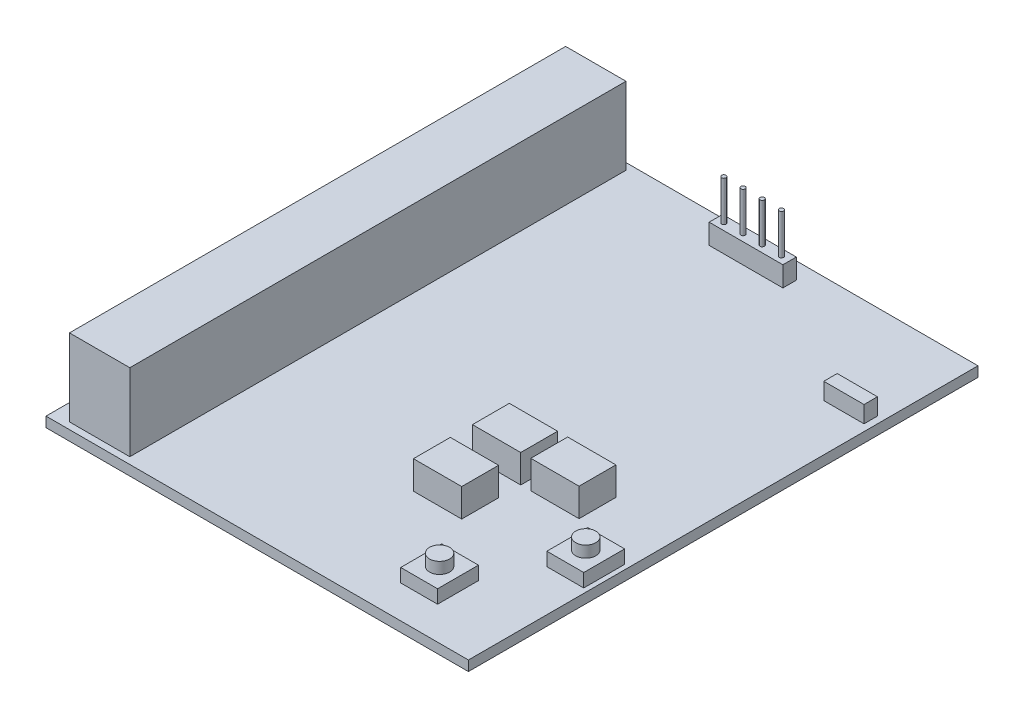
SolidWorks part; units mm, degrees
ref_plane "Front Plane" through (0, 0, 0) normal (0, 0, 1) x (1, 0, 0)
ref_plane "Top Plane" through (0, 0, 0) normal (0, 1, 0) x (1, 0, 0)
ref_plane "Right Plane" through (0, 0, 0) normal (1, 0, 0) x (0, 0, -1)
sketch "Sketch1" plane through (0, 0, 0) normal (0, 1, 0) x (1, 0, 0)
  line L1 (0, 0) -> (63, 0)
  line L2 (0, 0) -> (0, 76)
  line L3 (0, 76) -> (63, 76)
  line L4 (63, 0) -> (63, 76)
  dimension "D1" = 63
  dimension "D2" = 76
extrude "Boss-Extrude1" add sketch "Sketch1" along normal blind 1.5
sketch "Sketch2" plane through (0, 1.5, 0) normal (0, 1, 0) x (1, 0, 0)
  line L0 (63, 76) -> (0, 76) construction
  line L1 (2.5, 75) -> (11.5, 75)
  line L2 (2.5, 75) -> (2.5, 1)
  line L3 (2.5, 1) -> (11.5, 1)
  line L4 (11.5, 75) -> (11.5, 1)
  line L5 (0, 76) -> (0, 0) construction
  dimension "D1" = 74
  dimension "D2" = 1
  dimension "D3" = 2.5
  dimension "D4" = 9
extrude "Boss-Extrude2" add sketch "Sketch2" along normal blind 11.5
sketch "Sketch3" plane through (0, 0, 0) normal (0, -1, 0) x (1, 0, 0)
  line L0 (0, -76) -> (0, 0) construction
  line L1 (9, -15) -> (16, -15)
  line L2 (9, -15) -> (9, -23)
  line L3 (9, -23) -> (16, -23)
  line L4 (16, -15) -> (16, -23)
  line L5 (9, -34) -> (16, -34)
  line L6 (9, -34) -> (9, -42)
  line L7 (9, -42) -> (16, -42)
  line L8 (16, -34) -> (16, -42)
  line L9 (9, -56) -> (16, -56)
  line L10 (9, -56) -> (9, -64)
  line L11 (9, -64) -> (16, -64)
  line L12 (16, -56) -> (16, -64)
  line L13 (63, -76) -> (0, -76) construction
  dimension "D1" = 8
  dimension "D2" = 8
  dimension "D3" = 8
  dimension "D4" = 7
  dimension "D5" = 7
  dimension "D6" = 7
  dimension "D7" = 9
  dimension "D8" = 9
  dimension "D9" = 9
  dimension "D10" = 12
  dimension "D11" = 34
  dimension "D12" = 53
extrude "Boss-Extrude3" add sketch "Sketch3" along normal blind 3.5
sketch "Sketch4" plane through (0, 1.5, 0) normal (0, 1, 0) x (1, 0, 0)
  line L0 (63, 0) -> (63, 76) construction
  line L1 (27.4, 73.5) -> (38.4, 73.5)
  line L2 (27.4, 73.5) -> (27.4, 71.5)
  line L3 (27.4, 71.5) -> (38.4, 71.5)
  line L4 (38.4, 73.5) -> (38.4, 71.5)
  line L5 (63, 76) -> (0, 76) construction
  dimension "D1" = 11
  dimension "D2" = 2
  dimension "D3" = 24.6
  dimension "D4" = 2.5
extrude "Boss-Extrude4" add sketch "Sketch4" along normal blind 3
sketch "Sketch5" plane through (0, 4.5, 0) normal (0, 1, 0) x (1, 0, 0)
  line L0 (27.4, 73.5) -> (27.4, 71.5) construction
  line L1 (38.4, 73.5) -> (27.4, 73.5) construction
  circle A0 centre (28.6, 72.5) radius 0.325
  circle A1 centre (31.46, 72.5) radius 0.325
  circle A2 centre (34.32, 72.5) radius 0.325
  circle A3 centre (37.18, 72.5) radius 0.325
  dimension "D1" = 0.65
  dimension "D2" = 1.2
  dimension "D4" = 1
  dimension "D3" = 4
extrude "Boss-Extrude5" add sketch "Sketch5" along normal blind 6
sketch "Sketch6" plane through (0, 1.5, 0) normal (0, 1, 0) x (1, 0, 0)
  line L0 (63, 0) -> (63, 76) construction
  line L1 (56, 62) -> (62, 62)
  line L2 (56, 62) -> (56, 60)
  line L3 (56, 60) -> (62, 60)
  line L4 (62, 62) -> (62, 60)
  line L5 (63, 76) -> (0, 76) construction
  dimension "D1" = 6
  dimension "D2" = 2
  dimension "D3" = 1
  dimension "D4" = 14
extrude "Boss-Extrude6" add sketch "Sketch6" along normal blind 2.5
sketch "Sketch7" plane through (0, 4, 0) normal (0, 1, 0) x (1, 0, 0)
  line L0 (56, 62) -> (56, 60) construction
  circle A0 centre (57.5, 60.989) radius 0.4731
  circle A1 centre (60.4, 60.989) radius 0.4731
  dimension "D1" = 1.5
  dimension "D2" = 2
extrude "Boss-Extrude7" [suppressed] add sketch "Sketch7" along normal blind 6
sketch "Sketch8" plane through (0, 1.5, 0) normal (0, 1, 0) x (1, 0, 0)
  line L0 (63, 0) -> (63, 76) construction
  line L1 (37.1, 32) -> (44.3, 32)
  line L2 (37.1, 32) -> (37.1, 26.5)
  line L3 (37.1, 26.5) -> (44.3, 26.5)
  line L4 (44.3, 32) -> (44.3, 26.5)
  line L5 (45.8, 32) -> (53, 32)
  line L6 (45.8, 32) -> (45.8, 26.5)
  line L7 (45.8, 26.5) -> (53, 26.5)
  line L8 (53, 32) -> (53, 26.5)
  line L9 (37.1, 23.2) -> (44.3, 23.2)
  line L10 (37.1, 23.2) -> (37.1, 17.7)
  line L11 (37.1, 17.7) -> (44.3, 17.7)
  line L12 (44.3, 23.2) -> (44.3, 17.7)
  line L13 (0, 0) -> (63, 0) construction
  dimension "D1" = 7.2
  dimension "D2" = 7.2
  dimension "D3" = 7.2
  dimension "D4" = 5.5
  dimension "D5" = 5.5
  dimension "D6" = 5.5
  dimension "D7" = 10
  dimension "D8" = 18.7
  dimension "D9" = 18.7
  dimension "D10" = 17.7
  dimension "D11" = 26.5
  dimension "D12" = 26.5
extrude "Boss-Extrude8" add sketch "Sketch8" along normal blind 4.2
sketch "Sketch9" plane through (0, 1.5, 0) normal (0, 1, 0) x (1, 0, 0)
  line L0 (63, 0) -> (63, 76) construction
  line L1 (56.8, 24) -> (62.3, 24)
  line L2 (56.8, 24) -> (56.8, 17.9)
  line L3 (56.8, 17.9) -> (62.3, 17.9)
  line L4 (62.3, 24) -> (62.3, 17.9)
  line L5 (0, 0) -> (63, 0) construction
  dimension "D1" = 0.7
  dimension "D2" = 6.1
  dimension "D3" = 17.9
  dimension "D4" = 5.5
extrude "Boss-Extrude9" add sketch "Sketch9" along normal blind 2
sketch "Sketch10" plane through (0, 3.5, 0) normal (0, 1, 0) x (1, 0, 0)
  line L0 (62.3, 17.9) -> (62.3, 24) construction
  line L1 (62.3, 24) -> (56.8, 24) construction
  circle A0 centre (59.55, 20.95) radius 1.5
  dimension "D1" = 3
  dimension "D2" = 2.75
  dimension "D3" = 3.05
extrude "Boss-Extrude10" add sketch "Sketch10" along normal blind 1.7
sketch "Sketch11" plane through (0, 1.5, 0) normal (0, 1, 0) x (1, 0, 0)
  line L0 (63, 0) -> (63, 76) construction
  line L1 (48, 11) -> (53.5, 11)
  line L2 (48, 11) -> (48, 4.9)
  line L3 (48, 4.9) -> (53.5, 4.9)
  line L4 (53.5, 11) -> (53.5, 4.9)
  line L5 (0, 0) -> (63, 0) construction
  line L6 (56.8, 17.9) -> (62.3, 17.9) construction
  line L7 (62.3, 17.9) -> (62.3, 24) construction
  dimension "D1" = 9.5
  dimension "D2" = 4.9
extrude "Boss-Extrude11" add sketch "Sketch11" along normal blind 2
sketch "Sketch12" plane through (0, 3.5, 0) normal (0, 1, 0) x (1, 0, 0)
  line L0 (53.5, 4.9) -> (53.5, 11) construction
  line L1 (53.5, 11) -> (48, 11) construction
  circle A0 centre (50.75, 7.95) radius 1.5
  circle A1 centre (59.55, 20.95) radius 1.5 construction
  point P6 (50.75, 11)
  dimension "D1" = 2.75
  dimension "D2" = 3.05
extrude "Boss-Extrude12" add sketch "Sketch12" along normal blind 1.7 contours A0
